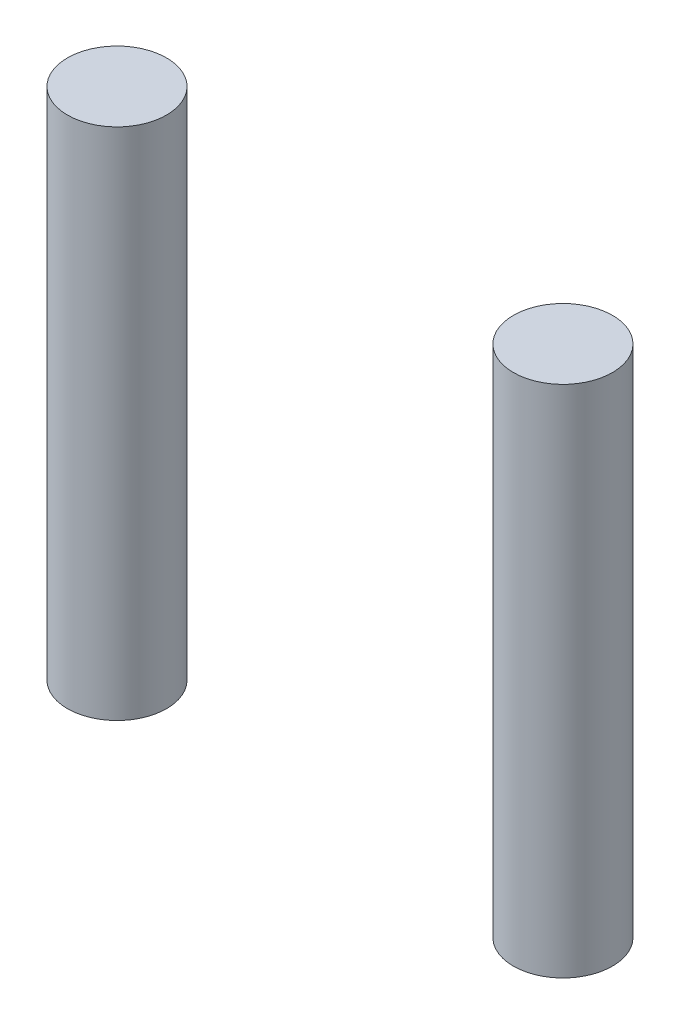
SolidWorks part; units mm, degrees
ref_plane "Front Plane" through (0, 0, 0) normal (0, 0, 1) x (1, 0, 0)
ref_plane "Top Plane" through (0, 0, 0) normal (0, 1, 0) x (1, 0, 0)
ref_plane "Right Plane" through (0, 0, 0) normal (1, 0, 0) x (0, 0, -1)
sketch "Sketch1" plane through (0, 0, 0) normal (0, 1, 0) x (1, 0, 0)
  line L0 (22.5, 0) -> (-22.5, 0) construction
  circle A0 centre (-22.5, 0) radius 5
  circle A1 centre (22.5, 0) radius 5
  point P4 (0, 0)
  point P7 (-27.5, 0)
  point P8 (27.5, 0)
  dimension "D1" = 10
  dimension "D2" = 55
extrude "Boss-Extrude1" add sketch "Sketch1" along normal blind 51.88
